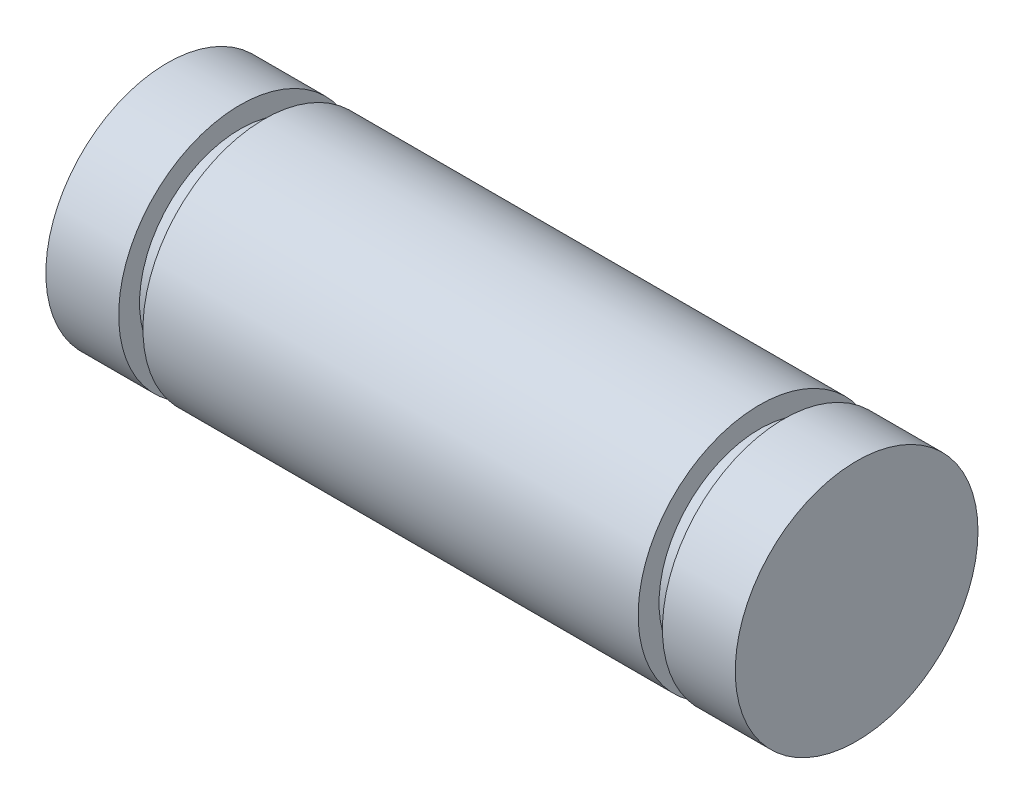
SolidWorks part; units mm, degrees
material "AISI 316 Annealed Stainless Steel Bar (SS)"
ref_plane "Front" through (0, 0, 0) normal (0, 0, 1) x (1, 0, 0)
ref_plane "Top" through (0, 0, 0) normal (0, 1, 0) x (1, 0, 0)
ref_plane "Right" through (0, 0, 0) normal (1, 0, 0) x (0, 0, -1)
sketch "Sketch1" plane through (0, 0, 0) normal (1, 0, 0) x (0, 0, -1)
  circle A0 centre (0, 0) radius 3.175
  dimension "D1" = 6.35
extrude "Extrude1" add sketch "Sketch1" along normal mid plane 18.034
sketch "Sketch2" plane through (0, 0, 0) normal (0, 0, 1) x (1, 0, 0)
  line L0 (9.017, 3.175) -> (-9.017, 3.175) construction
  line L1 (-7.112, 3.175) -> (-6.477, 3.175)
  line L2 (-7.112, 3.175) -> (-7.112, 2.6289)
  line L3 (-7.112, 2.6289) -> (-6.477, 2.6289)
  line L4 (-6.477, 3.175) -> (-6.477, 2.6289)
  line L5 (0, 0) -> (-5.2921, 0) construction
  line L6 (0, 0) -> (0, 4.4325) construction
  line L7 (6.477, 3.175) -> (6.477, 2.6289)
  line L8 (7.112, 2.6289) -> (6.477, 2.6289)
  line L9 (7.112, 3.175) -> (7.112, 2.6289)
  line L10 (7.112, 3.175) -> (6.477, 3.175)
  dimension "D1" = 12.954
  dimension "D2" = 0.635
  dimension "D3" = 5.2578
revolve "Cut-Revolve1" cut sketch "Sketch2" angle 360 about L5
